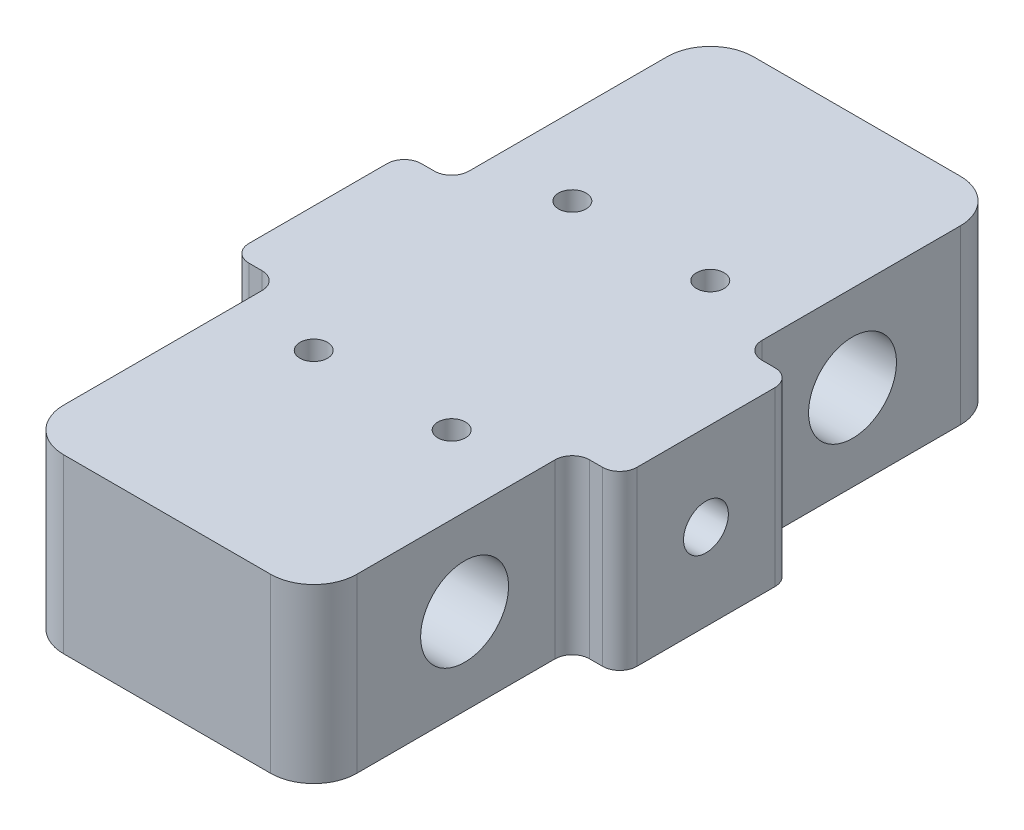
SolidWorks part; units mm, degrees
material "POM "
ref_plane "前视基准面" through (0, 0, 0) normal (0, 0, 1) x (1, 0, 0)
ref_plane "上视基准面" through (0, 0, 0) normal (0, 1, 0) x (1, 0, 0)
ref_plane "右视基准面" through (0, 0, 0) normal (1, 0, 0) x (0, 0, -1)
sketch "草图1" plane through (0, 0, 0) normal (0, 1, 0) x (1, 0, 0)
  line L0 (-8, -15) -> (8, -15) construction
  line L1 (-22.5, -40) -> (22.5, -40)
  line L2 (-22.5, -40) -> (-22.5, 40)
  line L3 (-22.5, 40) -> (22.5, 40)
  line L4 (22.5, -40) -> (22.5, 40)
  line L5 (0, 40) -> (0, -40) construction
  line L6 (-22.5, 0) -> (22.5, 0) construction
  line L7 (-8, -15) -> (-8, 15) construction
  line L8 (-8, 15) -> (8, 15) construction
  line L9 (8, -15) -> (8, 15) construction
  line L10 (0, 15) -> (0, -15) construction
  line L11 (-8, 0) -> (8, 0) construction
  circle A0 centre (8, 15) radius 1.6
  circle A1 centre (-8, 15) radius 1.6
  circle A2 centre (-8, -15) radius 1.6
  circle A3 centre (8, -15) radius 1.6
  circle A4 centre (8, 15) radius 1.4 construction
  circle A5 centre (-8, 15) radius 1.4 construction
  circle A6 centre (-8, -15) radius 1.4 construction
  circle A7 centre (8, -15) radius 1.4 construction
  point P0 (0, 0)
  point P15 (0, 0)
  dimension "D1" = 3.2
  dimension "D6" = 2.8
  dimension "D2" = 80
  dimension "D3" = 45
  dimension "D4" = 30
  dimension "D5" = 16
extrude "主体" add sketch "草图1" along normal blind 20
sketch "草图2" plane through (-22.5, 0, 0) normal (-1, 0, 0) x (0, 0, 1)
  line L1 (-40, 0) -> (40, 0) construction
  line L2 (-40, 0) -> (-40, 20) construction
  line L3 (-40, 20) -> (40, 20) construction
  line L4 (40, 0) -> (40, 20) construction
  line L5 (0, 20) -> (0, 0) construction
  line L6 (-40, 10) -> (40, 10) construction
  circle A0 centre (0, 10) radius 2.6
  point P0 (0, 10)
  dimension "D1" = 5.2
extrude "调节孔" cut sketch "草图2" against normal through all
sketch "草图3" plane through (-22.5, 0, 0) normal (-1, 0, 0) x (0, 0, 1)
  line L0 (-970, 10) -> (49030, 10) construction
  line L1 (40, 20) -> (40, 0) construction
  line L2 (0, -1000) -> (0, 49000) construction
  circle A0 centre (22.5, 10) radius 5.1
  circle A1 centre (-22.5, 10) radius 5.1
  point P5 (40, 10)
  dimension "D1" = 10.2
  dimension "D2" = 45
extrude "转轴孔" cut sketch "草图3" against normal through all
sketch "草图5" plane through (-22.5, 0, 0) normal (-1, 0, 0) x (0, 0, 1)
  line L0 (-40, 20) -> (40, 20) construction
  line L1 (40, 20) -> (10, 20)
  line L2 (40, 20) -> (40, 0)
  line L3 (40, 0) -> (10, 0)
  line L4 (10, 20) -> (10, 0)
  line L5 (-40, 0) -> (40, 0) construction
  line L6 (40, 20) -> (40, 0) construction
  circle A0 centre (22.5, 10) radius 9.25 construction
  dimension "D1" = 18.5
  dimension "D2" = 30
extrude "推力轴承" cut sketch "草图5" against normal blind 5.5
mirror "镜向1" about plane through (0, 0, 0) normal (1, 0, 0) of "推力轴承"
mirror "镜向2" about plane through (0, 0, 0) normal (0, 0, 1) of "镜向1", "推力轴承"
fillet "圆角2" radius 2 8 edges at (22.5, 10, -10) (17, 10, -10) (22.5, 10, 10) (17, 10, 10) (-17, 10, -10) (-22.5, 10, -10) (-22.5, 10, 10) (-17, 10, 10)
fillet "圆角5" radius 5 4 edges at (17, 10, -40) (-17, 10, -40) (17, 10, 40) (-17, 10, 40)
